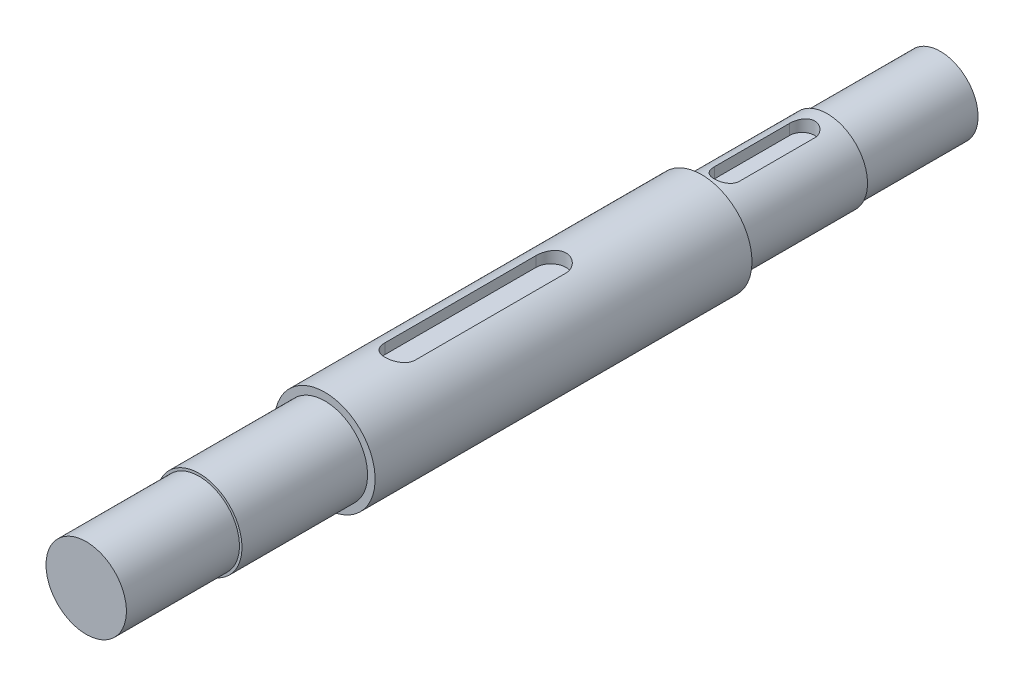
SolidWorks part; units mm, degrees
material "AISI 1020"
ref_plane "Front Plane" through (0, 0, 0) normal (0, 0, 1) x (1, 0, 0)
ref_plane "Top Plane" through (0, 0, 0) normal (0, 1, 0) x (1, 0, 0)
ref_plane "Right Plane" through (0, 0, 0) normal (1, 0, 0) x (0, 0, -1)
sketch "Sketch1" plane through (0, 0, 0) normal (0, 1, 0) x (1, 0, 0)
  line L0 (0, 0) -> (0, -265)
  line L3 (15, -45) -> (16, -45)
  line L4 (16, -45) -> (16, -95)
  line L7 (16, -95) -> (20, -95)
  line L8 (20, -95) -> (20, -245)
  line L9 (20, -245) -> (17, -245)
  line L12 (15, -45) -> (15, 0)
  line L13 (15, 0) -> (0, 0)
  line L14 (17, -245) -> (17, -295)
  line L15 (17, -295) -> (16, -295)
  line L16 (16, -295) -> (16, -340)
  line L17 (16, -340) -> (0, -340)
  line L18 (0, -340) -> (0, -265)
  dimension "D1" = 340
  dimension "D2" = 17
  dimension "D3" = 50
  dimension "D4" = 16
  dimension "D5" = 150
  dimension "D6" = 45
  dimension "D7" = 1
  dimension "D8" = 20
revolve "Revolve1" add sketch "Sketch1" angle 360 about L0
sketch "Sketch2" plane through (-4.4668, 29.5948, 45) normal (0, 0, -1) x (-1, 0, 0)
  line L0 (-4.4668, -13.5948) -> (-4.4668, -29.5948) construction
  line L1 (-4.4668, -29.5948) -> (-4.4668, -13.5948) construction
  circle A0 centre (-4.4668, -29.5948) radius 16 construction
  circle A2 centre (-4.4668, -29.5948) radius 16
  dimension "Angle from vertical" = 360
ref_plane "Plane1" through (0, 16, 45) normal (0, -1, 0) x (-1, 0, 0)
sketch "Sketch3" plane through (2.2334, 16, 45) normal (0, -1, 0) x (0, 0, -1)
  line L0 (-10, -2.2334) -> (-40, -2.2334) construction
  line L1 (-10, 2.7666) -> (-40, 2.7666)
  line L2 (-10, -7.2334) -> (-40, -7.2334)
  arc A0 (-10, 2.7666) -> (-10, -7.2334) centre (-10, -2.2334) cw
  arc A1 (-40, 2.7666) -> (-40, -7.2334) centre (-40, -2.2334) ccw
  dimension "Keyway width" = 10
  dimension "Distance from end face" = 10
  dimension "Length of slot" = 30
extrude "Cut-Extrude1" cut sketch "Sketch3" along normal blind 5
other "keyway (bs 4235 - part i)<1>"
sketch "Sketch21" plane through (-2.2756, 37.0318, 245) normal (0, 0, 1) x (1, 0, 0)
  line L0 (2.2756, -17.0318) -> (2.2756, -37.0318) construction
  line L1 (2.2756, -37.0318) -> (2.2756, -17.0318) construction
  circle A0 centre (2.2756, -37.0318) radius 20 construction
  circle A2 centre (2.2756, -37.0318) radius 20
  dimension "Angle from vertical" = 0
ref_plane "Plane11" through (0, 20, 245) normal (0, -1, 0) x (-1, 0, 0)
sketch "Sketch31" plane through (1.1378, 20, 245) normal (0, -1, 0) x (0, 0, 1)
  line L0 (-30, 1.1378) -> (-90, 1.1378) construction
  line L1 (-30, 7.1378) -> (-90, 7.1378)
  line L2 (-30, -4.8622) -> (-90, -4.8622)
  arc A0 (-30, 7.1378) -> (-30, -4.8622) centre (-30, 1.1378) cw
  arc A1 (-90, 7.1378) -> (-90, -4.8622) centre (-90, 1.1378) ccw
  dimension "Keyway width" = 12
  dimension "Distance from end face" = 30
  dimension "Length of slot" = 60
extrude "Cut-Extrude11" cut sketch "Sketch31" along normal blind 5
other "keyway (bs 4235 - part i)<2>"
